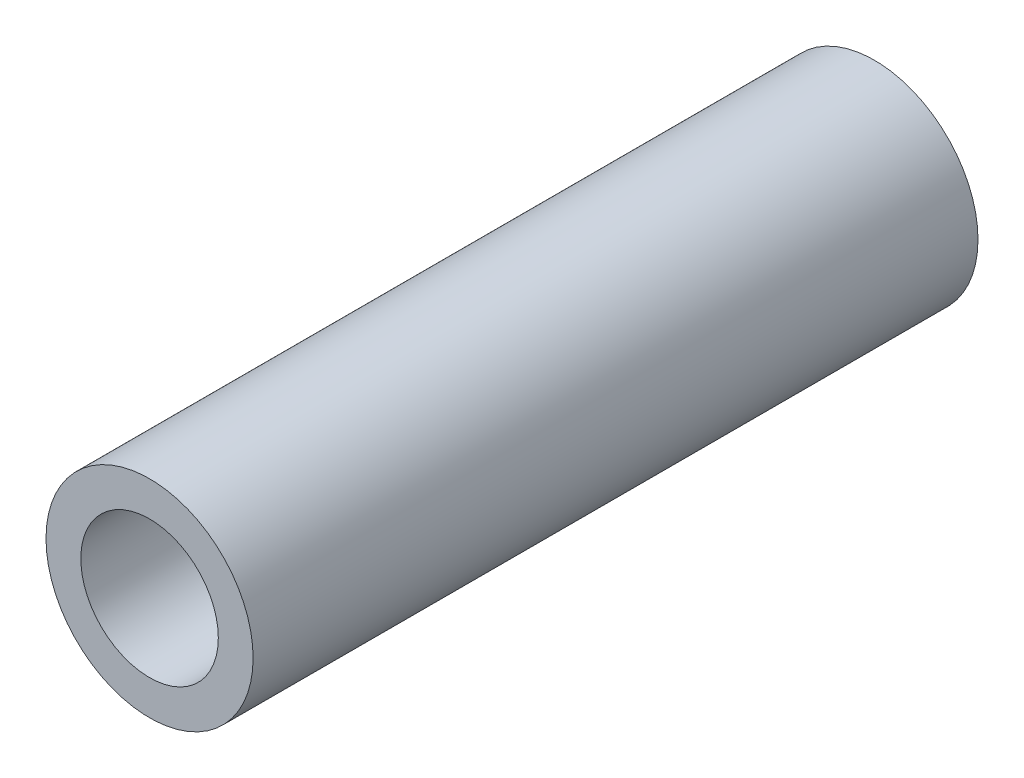
SolidWorks part; units mm, degrees
ref_plane "Front Plane" through (0, 0, 0) normal (0, 0, 1) x (1, 0, 0)
ref_plane "Top Plane" through (0, 0, 0) normal (0, 1, 0) x (1, 0, 0)
ref_plane "Right Plane" through (0, 0, 0) normal (1, 0, 0) x (0, 0, -1)
sketch "Sketch1" plane through (0, 0, 0) normal (0, 0, 1) x (1, 0, 0)
  circle A0 centre (0, 0) radius 3.175
  circle A1 centre (0, 0) radius 2.1082
  dimension "OD" = 6.35
  dimension "ID" = 4.2164
extrude "Extrude1" add sketch "Sketch1" along normal mid plane 22.225
sketch "Sketch2" plane through (0, 0, 0) normal (1, 0, 0) x (0, 0, -1)
  line L0 (-11.1125, -2.1082) -> (11.1125, -2.1082) construction
  line L3 (11.1125, 2.1082) -> (-11.1125, 2.1082) construction
  line L5 (-11.1125, -2.1082) -> (11.1125, -2.1082)
  line L6 (11.1125, 2.1082) -> (-11.1125, 2.1082)
sketch "Sketch4" plane through (0, 0, 11.1125) normal (0, 0, 1) x (1, 0, 0)
  line L0 (0, 0) -> (-1.4907, 1.4907)
  line L1 (0, -2.1828) -> (0, 2.1828) construction
  circle A0 centre (0, 0) radius 2.1082 construction
  dimension "D1" = 45
